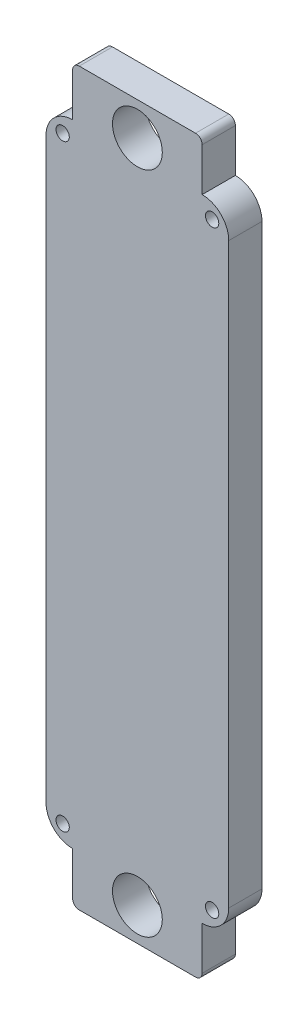
SolidWorks part; units mm, degrees
ref_plane "Plano frontal" through (0, 0, 0) normal (0, 0, 1) x (1, 0, 0)
ref_plane "Plano superior" through (0, 0, 0) normal (0, 1, 0) x (1, 0, 0)
ref_plane "Plano direito" through (0, 0, 0) normal (1, 0, 0) x (0, 0, -1)
sketch "Esboço1" plane through (0, 0, 0) normal (0, 0, 1) x (1, 0, 0)
  line L1 (-27.5, 95) -> (27.5, 95)
  line L2 (-27.5, 95) -> (-27.5, -95)
  line L3 (-27.5, -95) -> (27.5, -95)
  line L4 (27.5, 95) -> (27.5, -95)
  line L5 (-27.5, 95) -> (27.5, -95) construction
  line L6 (-27.5, -95) -> (27.5, 95) construction
  circle A0 centre (-22.5, 90) radius 2
  circle A1 centre (22.5, 90) radius 2
  circle A2 centre (-22.5, -90) radius 2
  circle A3 centre (22.5, -90) radius 2
  point P0 (0, 0)
  dimension "D3" = 5
  dimension "D4" = 5
  dimension "D5" = 4
  dimension "D6" = 4
  dimension "D7" = 4
  dimension "D8" = 4
  dimension "D9" = 5
  dimension "D10" = 5
  dimension "D11" = 5
  dimension "D12" = 5
  dimension "D13" = 5
  dimension "D14" = 5
  dimension "D1" = 190
  dimension "D2" = 55
extrude "Ressalto-extrusão1" add sketch "Esboço1" along normal blind 10
fillet "Filete1" radius 8 4 edges at (-27.5, -95, 5) (27.5, -95, 5) (27.5, 95, 5) (-27.5, 95, 5)
sketch "Esboço3" plane through (0, 0, 10) normal (0, 0, 1) x (1, 0, 0)
  line L0 (-19.5, 95) -> (19.5, 95)
  line L1 (-19.5, 95) -> (-19.5, 110)
  line L2 (19.5, 95) -> (19.5, 110)
  line L3 (-19.5, 110) -> (19.5, 110)
  line L4 (-19.5, -95) -> (19.5, -95)
  line L5 (-19.5, -95) -> (-19.5, -110)
  line L6 (19.5, -95) -> (19.5, -110)
  line L7 (-19.5, -110) -> (19.5, -110)
  dimension "D1" = 15
  dimension "D2" = 15
extrude "Ressalto-extrusão2" add sketch "Esboço3" against normal blind 10
sketch "Esboço4" plane through (0, 0, 10) normal (0, 0, 1) x (1, 0, 0)
  line L0 (-19.5, -110) -> (19.5, -110) construction
  line L1 (19.5, 110) -> (-19.5, 110) construction
  circle A0 centre (0, 100) radius 7.5
  circle A1 centre (0, -100) radius 7.5
  dimension "D1" = 15
  dimension "D2" = 15
  dimension "D3" = 10
  dimension "D4" = 10
extrude "Corte-extrusão2" cut sketch "Esboço4" against normal blind 10
fillet "Filete2" radius 2 4 edges at (-19.5, 110, 5) (19.5, 110, 5) (-19.5, -110, 5) (19.5, -110, 5)
